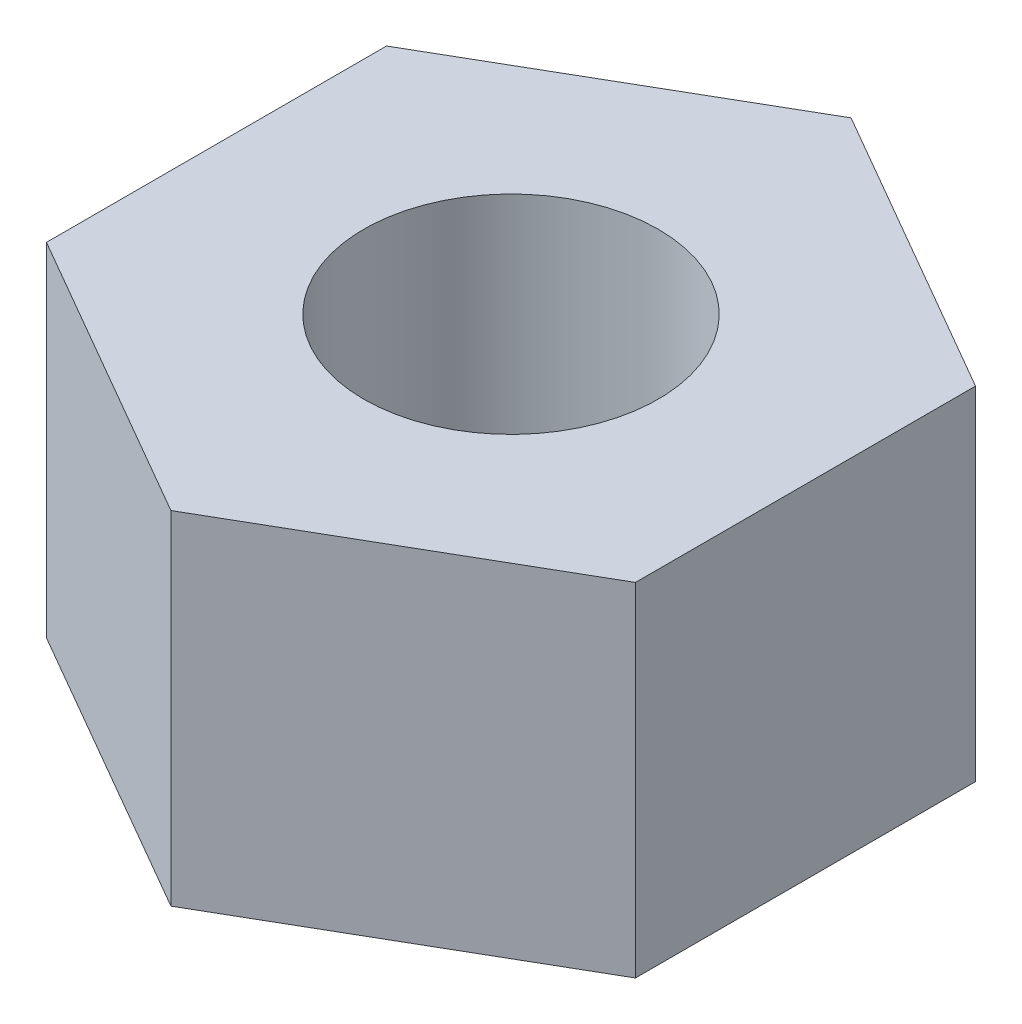
SolidWorks part; units mm, degrees
ref_plane "Front Plane" through (0, 0, 0) normal (0, 0, 1) x (1, 0, 0)
ref_plane "Top Plane" through (0, 0, 0) normal (0, 1, 0) x (1, 0, 0)
ref_plane "Right Plane" through (0, 0, 0) normal (1, 0, 0) x (0, 0, -1)
sketch "Sketch1" plane through (0, 0, 0) normal (0, 1, 0) x (1, 0, 0)
  line L1 (0, -2.2632) -> (1.96, -1.1316)
  line L2 (1.96, -1.1316) -> (1.96, 1.1316)
  line L3 (1.96, 1.1316) -> (0, 2.2632)
  line L4 (0, 2.2632) -> (-1.96, 1.1316)
  line L5 (-1.96, 1.1316) -> (-1.96, -1.1316)
  line L6 (-1.96, -1.1316) -> (0, -2.2632)
  circle A0 centre (0, 0) radius 1.96 construction
  circle A1 centre (0, 0) radius 0.98
  dimension "D1" = 1.96
  dimension "D2" = 3.92
extrude "Boss-Extrude1" add sketch "Sketch1" along normal blind 2.28
